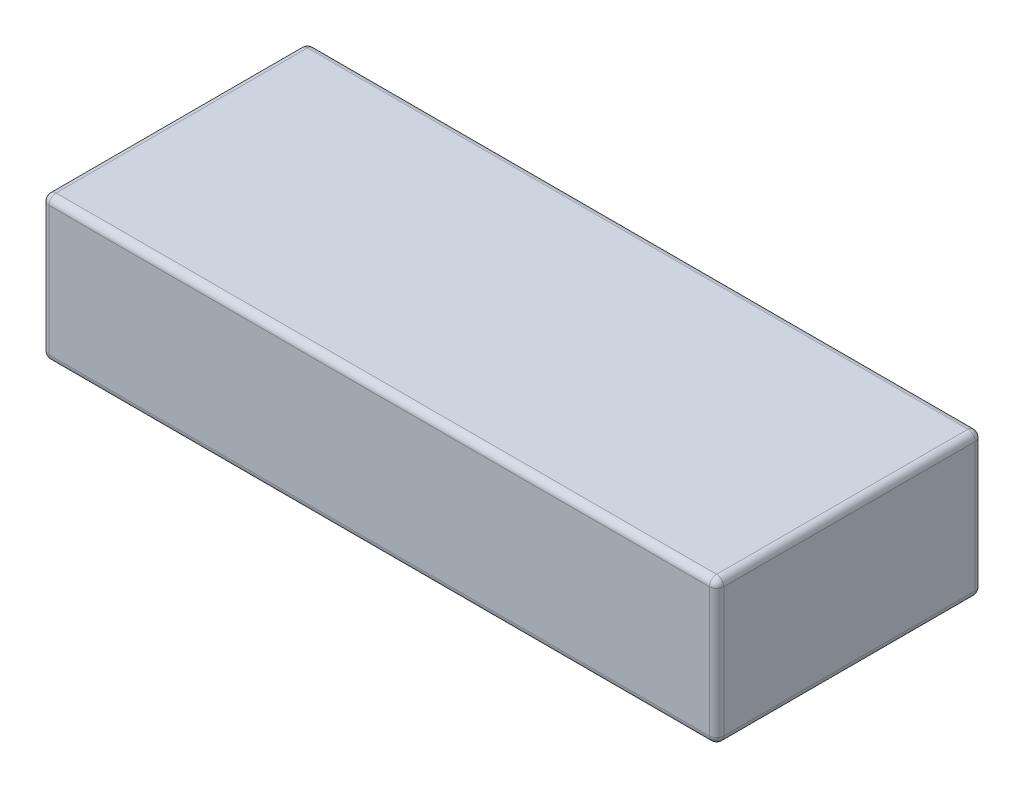
SolidWorks part; units mm, degrees
ref_plane "Alzado" through (0, 0, 0) normal (0, 0, 1) x (1, 0, 0)
ref_plane "Planta" through (0, 0, 0) normal (0, 1, 0) x (1, 0, 0)
ref_plane "Vista lateral" through (0, 0, 0) normal (1, 0, 0) x (0, 0, -1)
sketch "Croquis1" plane through (0, 0, 0) normal (0, 1, 0) x (1, 0, 0)
  line L1 (0, 0) -> (94, 0)
  line L2 (0, 0) -> (0, 37)
  line L3 (0, 37) -> (94, 37)
  line L4 (94, 0) -> (94, 37)
  dimension "D1" = 94
  dimension "D2" = 37
extrude "Saliente-Extruir1" add sketch "Croquis1" along normal blind 20
fillet "Redondeo1" radius 1 12 edges at (0, 10, 0) (94, 10, 0) (94, 10, -37) (0, 10, -37) (47, 20, -37) (94, 20, -18.5) (47, 20, 0) (0, 20, -18.5) (47, 0, -37) (94, 0, -18.5) (47, 0, 0) (0, 0, -18.5)
